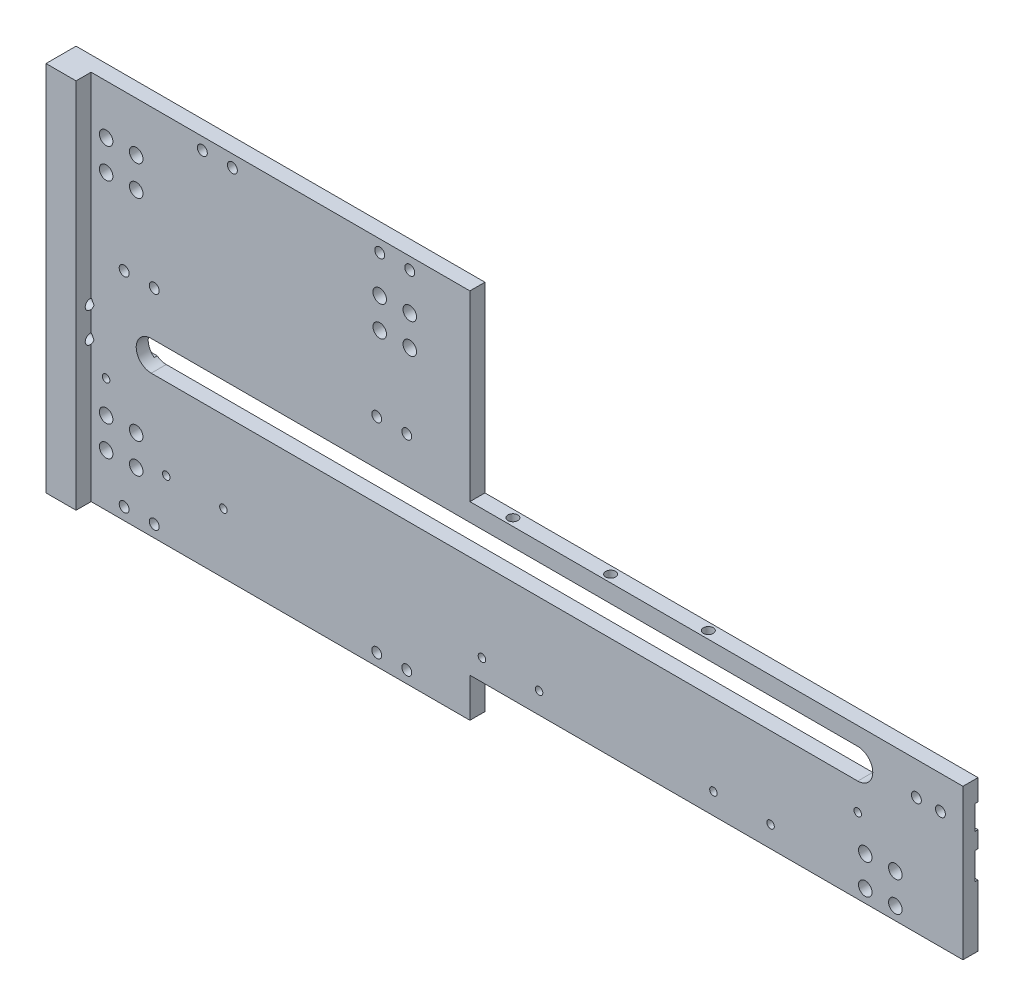
SolidWorks part; units mm, degrees
ref_plane "前视基准面" through (0, 0, 0) normal (0, 0, 1) x (1, 0, 0)
ref_plane "上视基准面" through (0, 0, 0) normal (0, 1, 0) x (1, 0, 0)
ref_plane "右视基准面" through (0, 0, 0) normal (1, 0, 0) x (0, 0, -1)
sketch "草图4" plane through (0, 0, 0) normal (0, 0, 1) x (1, 0, 0)
  line L0 (30, 99.7) -> (265, 99.7) construction
  line L1 (0, 0) -> (136, 0)
  line L2 (0, 0) -> (0, 123.7)
  line L3 (0, 123.7) -> (136, 123.7)
  line L4 (300, 60.7) -> (300, 110.7)
  line L5 (30, 104.7) -> (265, 104.7)
  line L6 (136, 123.7) -> (136, 110.7)
  line L7 (136, 110.7) -> (300, 110.7)
  line L9 (30, 94.7) -> (265, 94.7)
  line L10 (136, 0) -> (136, 60.7)
  line L11 (136, 60.7) -> (300, 60.7)
  arc A0 (30, 104.7) -> (30, 94.7) centre (30, 99.7) ccw
  arc A1 (265, 94.7) -> (265, 104.7) centre (265, 99.7) ccw
  dimension "D1" = 300
  dimension "D2" = 136
  dimension "D3" = 13
  dimension "D4" = 63
  dimension "D5" = 123.7
  dimension "D6" = 10
  dimension "D7" = 30
  dimension "D8" = 265
  dimension "D9" = 24
extrude "凸台-拉伸1" add sketch "草图4" along normal blind 10
sketch "草图5" plane through (300, 0, 0) normal (1, 0, 0) x (0, 0, -1)
  line L1 (0, 60.7) -> (0, 110.7) construction
  line L2 (-10, 123.7) -> (0, 123.7) construction
  line L3 (0, 103.7) -> (-1, 103.7)
  line L4 (0, 103.7) -> (0, 95.7)
  line L6 (0, 95.7) -> (-1, 95.7)
  line L7 (0, 90.2) -> (-1, 90.2)
  line L8 (0, 90.2) -> (0, 81.2)
  line L9 (0, 81.2) -> (-1, 81.2)
  line L10 (-1, 90.2) -> (-1, 81.2)
  line L12 (-1, 103.7) -> (-1, 95.7)
  dimension "D1" = 20
  dimension "D2" = 8
  dimension "D3" = 33.5
  dimension "D4" = 9
  dimension "D5" = 1
extrude "切除-拉伸1" cut sketch "草图5" against normal through all
hole_wizard "M4 螺纹孔1" positions "草图6" profile "草图7" tap size "M4" standard "ISO"
sketch "草图6" plane through (0, 0, 0) normal (-1, 0, 0) x (0, 0, 1)
  line L0 (10, 123.7) -> (10, 0) construction
  line L1 (10, 123.7) -> (0, 123.7) construction
  point P0 (5.304, 104.7)
  point P2 (5.304, 94.7)
  dimension "D1" = 4.696
  dimension "D2" = 19
  dimension "D3" = 29
sketch "草图7" plane through (0, 104.7, 5.304) normal (0, 1, 0) x (0, 0, 1)
  line L0 (0, 0) -> (0, 11.0914)
  line L1 (0, 11.0914) -> (1.65, 10.1)
  line L2 (1.65, 10.1) -> (1.65, 0)
  line L5 (1.65, 0) -> (0, 0)
  line L10 (0, 11.0914) -> (-1.65, 10.1) construction
  line L11 (0, -6.35) -> (0, 107.95) construction
  dimension "螺纹孔钻头直径" = 3.3
  dimension "螺纹孔钻头深度" = 10.1
  dimension "导头角度" = 118
cosmetic thread "孔螺蚊线1" parameters "D1"=8, "D2"=4
cosmetic thread "孔螺蚊线2" parameters "D1"=8, "D2"=4
sketch "草图8" plane through (0, 0, 10) normal (0, 0, 1) x (1, 0, 0)
  line L1 (136, 123.7) -> (0, 123.7) construction
  line L2 (10, 123.7) -> (316.5249, 123.7)
  line L3 (10, 123.7) -> (10, -39.0626)
  line L4 (10, -39.0626) -> (316.5249, -39.0626)
  line L5 (316.5249, 123.7) -> (316.5249, -39.0626)
  line L6 (0, 123.7) -> (0, 0) construction
  dimension "D1" = 10
extrude "切除-拉伸2" cut sketch "草图8" against normal blind 5
hole_wizard "M4 螺纹孔2" positions "草图9" profile "草图10" tap size "M4" standard "ISO"
sketch "草图9" plane through (0, 0, 5) normal (0, 0, 1) x (1, 0, 0)
  line L0 (136, 123.7) -> (10, 123.7) construction
  line L1 (0, 123.7) -> (0, 0) construction
  point P0 (21, 119.7)
  point P2 (31, 119.7)
  point P4 (105, 119.7)
  point P6 (115, 119.7)
  point P8 (21, 51.7)
  point P10 (31, 51.7)
  point P12 (105, 51.7)
  point P14 (115, 51.7)
  point P16 (47, 4)
  point P18 (57, 4)
  point P20 (106, 4)
  point P22 (116, 4)
  dimension "D1" = 4
  dimension "D2" = 72
  dimension "D3" = 119.7
  dimension "D4" = 21
  dimension "D5" = 31
  dimension "D6" = 105
  dimension "D7" = 115
  dimension "D8" = 47
  dimension "D9" = 57
  dimension "D10" = 106
  dimension "D11" = 116
sketch "草图10" plane through (21, 119.7, 5) normal (1, 0, 0) x (0, -1, 0)
  line L0 (0, 0) -> (0, 11.0914)
  line L1 (0, 11.0914) -> (1.65, 10.1)
  line L2 (1.65, 10.1) -> (1.65, 0)
  line L5 (1.65, 0) -> (0, 0)
  line L10 (0, 11.0914) -> (-1.65, 10.1) construction
  line L11 (0, -6.35) -> (0, 107.95) construction
  dimension "螺纹孔钻头直径" = 3.3
  dimension "螺纹孔钻头深度" = 10.1
  dimension "导头角度" = 118
cosmetic thread "孔螺蚊线3" parameters "D1"=5, "D2"=4
cosmetic thread "孔螺蚊线4" parameters "D1"=5, "D2"=4
cosmetic thread "孔螺蚊线5" parameters "D1"=5, "D2"=4
cosmetic thread "孔螺蚊线6" parameters "D1"=5, "D2"=4
cosmetic thread "孔螺蚊线7" parameters "D1"=5, "D2"=4
cosmetic thread "孔螺蚊线8" parameters "D1"=5, "D2"=4
cosmetic thread "孔螺蚊线9" parameters "D1"=5, "D2"=4
cosmetic thread "孔螺蚊线10" parameters "D1"=5, "D2"=4
cosmetic thread "孔螺蚊线11" parameters "D1"=5, "D2"=4
cosmetic thread "孔螺蚊线12" parameters "D1"=5, "D2"=4
cosmetic thread "孔螺蚊线13" parameters "D1"=5, "D2"=4
cosmetic thread "孔螺蚊线14" parameters "D1"=5, "D2"=4
hole_wizard "M3 螺纹孔1" positions "草图11" profile "草图12" tap size "M3" standard "ISO"
sketch "草图11" plane through (0, 0, 5) normal (0, 0, 1) x (1, 0, 0)
  line L0 (0, 123.7) -> (0, 0) construction
  line L1 (10, 123.7) -> (0, 123.7) construction
  point P0 (15, 85.7)
  point P2 (265, 85.7)
  dimension "D1" = 15
  dimension "D2" = 265
  dimension "D3" = 38
sketch "草图12" plane through (15, 85.7, 5) normal (1, 0, 0) x (0, -1, 0)
  line L0 (0, 0) -> (0, 8.2511)
  line L1 (0, 8.2511) -> (1.25, 7.5)
  line L2 (1.25, 7.5) -> (1.25, 0)
  line L5 (1.25, 0) -> (0, 0)
  line L10 (0, 8.2511) -> (-1.25, 7.5) construction
  line L11 (0, -6.35) -> (0, 107.95) construction
  dimension "螺纹孔钻头直径" = 2.5
  dimension "螺纹孔钻头深度" = 7.5
  dimension "导头角度" = 118
cosmetic thread "孔螺蚊线15" parameters "D1"=4, "D2"=3
cosmetic thread "孔螺蚊线16" parameters "D1"=4, "D2"=3
hole_wizard "M3 螺纹孔2" positions "草图13" profile "草图14" tap size "M3" standard "ISO"
sketch "草图13" plane through (0, 0, 5) normal (0, 0, 1) x (1, 0, 0)
  line L0 (136, 123.7) -> (10, 123.7) construction
  line L1 (0, 123.7) -> (0, 0) construction
  point P0 (35, 67.7)
  point P2 (54, 67.7)
  point P4 (140, 67.7)
  point P6 (159, 67.7)
  point P8 (217, 67.7)
  point P10 (236, 67.7)
  dimension "D1" = 56
  dimension "D2" = 35
  dimension "D3" = 54
  dimension "D4" = 140
  dimension "D5" = 159
  dimension "D6" = 217
  dimension "D7" = 236
sketch "草图14" plane through (35, 67.7, 5) normal (1, 0, 0) x (0, -1, 0)
  line L0 (0, 0) -> (0, 8.2511)
  line L1 (0, 8.2511) -> (1.25, 7.5)
  line L2 (1.25, 7.5) -> (1.25, 0)
  line L5 (1.25, 0) -> (0, 0)
  line L10 (0, 8.2511) -> (-1.25, 7.5) construction
  line L11 (0, -6.35) -> (0, 107.95) construction
  dimension "螺纹孔钻头直径" = 2.5
  dimension "螺纹孔钻头深度" = 7.5
  dimension "导头角度" = 118
cosmetic thread "孔螺蚊线17" parameters "D1"=5, "D2"=3
cosmetic thread "孔螺蚊线18" parameters "D1"=5, "D2"=3
cosmetic thread "孔螺蚊线19" parameters "D1"=5, "D2"=3
cosmetic thread "孔螺蚊线20" parameters "D1"=5, "D2"=3
cosmetic thread "孔螺蚊线21" parameters "D1"=5, "D2"=3
cosmetic thread "孔螺蚊线22" parameters "D1"=5, "D2"=3
sketch "草图15" plane through (0, 0, 5) normal (0, 0, 1) x (1, 0, 0)
  line L0 (0, 123.7) -> (0, 0) construction
  line L1 (136, 123.7) -> (10, 123.7) construction
  line L2 (20, 75) -> (20, 133.6461) construction
  line L3 (4.9076, 70) -> (26.7652, 70) construction
  circle A0 centre (15, 75) radius 2.25
  circle A1 centre (25, 75) radius 2.25
  circle A2 centre (25, 65) radius 2.25
  circle A3 centre (15, 65) radius 2.25
  dimension "D1" = 4.5
  dimension "D2" = 15
  dimension "D3" = 48.7
  dimension "D4" = 5
  dimension "D5" = 5
extrude "切除-拉伸3" cut sketch "草图15" against normal blind 5
pattern_linear "阵列(线性)1" count 2 spacing 252.5 along (1, 0, 0) of "切除-拉伸3"
pattern_linear "阵列(线性)2" count 2 spacing 35 along (0, -1, 0) of "切除-拉伸3"
pattern_linear "阵列(线性)3" count 2 spacing 100 along (1, 0, 0) of "阵列(线性)2", "切除-拉伸3"
sketch "草图16" plane through (0, 0, 5) normal (0, 0, 1) x (1, 0, 0)
  line L1 (105.3882, 81.0569) -> (130.1902, 81.0569)
  line L2 (105.3882, 81.0569) -> (105.3882, 58.9705)
  line L3 (105.3882, 58.9705) -> (130.1902, 58.9705)
  line L4 (130.1902, 81.0569) -> (130.1902, 58.9705)
extrude "凸台-拉伸2" add sketch "草图16" against normal up to surface (5 mm away) up to face at (122.75, 75, 0)
hole_wizard "M4 螺纹孔3" positions "草图17" profile "草图18" tap size "M4" standard "ISO"
sketch "草图17" plane through (0, 60.7, 0) normal (0, -1, 0) x (-1, 0, 0)
  line L0 (-136, -5) -> (-300, -5) construction
  line L1 (0, -10) -> (0, 0) construction
  point P0 (-147.8, -2.5)
  point P2 (-180.3, -2.5)
  point P4 (-212.8, -2.5)
  dimension "D1" = 2.5
  dimension "D2" = 147.8
  dimension "D3" = 180.3
  dimension "D4" = 212.8
sketch "草图18" plane through (147.8, 60.7, 2.5) normal (1, 0, 0) x (0, 0, -1)
  line L0 (0, 0) -> (0, 11.0914)
  line L1 (0, 11.0914) -> (1.65, 10.1)
  line L2 (1.65, 10.1) -> (1.65, 0)
  line L5 (1.65, 0) -> (0, 0)
  line L10 (0, 11.0914) -> (-1.65, 10.1) construction
  line L11 (0, -6.35) -> (0, 107.95) construction
  dimension "螺纹孔钻头直径" = 3.3
  dimension "螺纹孔钻头深度" = 10.1
  dimension "导头角度" = 118
cosmetic thread "孔螺蚊线23" parameters "D1"=8, "D2"=4
cosmetic thread "孔螺蚊线24" parameters "D1"=8, "D2"=4
cosmetic thread "孔螺蚊线25" parameters "D1"=8, "D2"=4
ref_plane "基准面1" through (0, 85.7, 0) normal (0, -1, 0) x (-1, 0, 0)
mirror "镜向1" about plane through (0, 85.7, 0) normal (0, -1, 0) of "M4 螺纹孔3"
hole_wizard "M4 螺纹孔4" positions "草图19" profile "草图20" tap size "M4" standard "ISO"
sketch "草图19" plane through (0, 0, 1) normal (0, 0, -1) x (-1, 0, 0)
  line L0 (-300, 103.7) -> (-300, 95.7) construction
  line L1 (-268, 95.7) -> (-300, 95.7) construction
  point P0 (-284.5, 99.7)
  point P2 (-292.5, 99.7)
  dimension "D1" = 8
  dimension "D2" = 7.5
  dimension "D3" = 4
sketch "草图20" plane through (284.5, 99.7, 1) normal (1, 0, 0) x (0, 1, 0)
  line L0 (0, 0) -> (0, 11.0914)
  line L1 (0, 11.0914) -> (1.65, 10.1)
  line L2 (1.65, 10.1) -> (1.65, 0)
  line L5 (1.65, 0) -> (0, 0)
  line L10 (0, 11.0914) -> (-1.65, 10.1) construction
  line L11 (0, -6.35) -> (0, 107.95) construction
  dimension "螺纹孔钻头直径" = 3.3
  dimension "螺纹孔钻头深度" = 10.1
  dimension "导头角度" = 118
cosmetic thread "孔螺蚊线26" parameters "D1"=4, "D2"=4
cosmetic thread "孔螺蚊线27" parameters "D1"=4, "D2"=4
sketch "草图21" plane through (0, 123.7, 0) normal (0, 1, 0) x (1, 0, 0)
  line L0 (0, -10) -> (0, 0)
  line L1 (0, 0) -> (136, 0)
  line L2 (136, 0) -> (136, -5)
  line L3 (136, -5) -> (10, -5)
  line L4 (10, -5) -> (10, -10)
  line L5 (10, -10) -> (0, -10)
extrude "凸台-拉伸3" add sketch "草图21" along normal blind 47.7
ref_plane "基准面2" through (0, 85.7, 0) normal (0, -1, 0) x (-1, 0, 0)
mirror "镜向2" about plane through (0, 85.7, 0) normal (0, -1, 0) of "M4 螺纹孔2"
sketch "草图24" plane through (0, 0, 0) normal (0, 0, -1) x (-1, 0, 0)
  line L0 (0, 81.2) -> (0, 0) construction
  line L1 (0, 47.7) -> (-146.6221, 47.7)
  line L2 (0, 47.7) -> (0, -36.9879)
  line L3 (0, -36.9879) -> (-146.6221, -36.9879)
  line L4 (-146.6221, 47.7) -> (-146.6221, -36.9879)
  line L5 (0, 47.7) -> (-134.6, 47.7) construction
extrude "切除-拉伸4" cut sketch "草图24" against normal blind 47.7
pattern_linear "阵列(线性)4" count 2 spacing 80 along (0, 1, 0) of "切除-拉伸3"
sketch "草图25" plane through (0, 0, 0) normal (0, 0, -1) x (-1, 0, 0)
  line L0 (-15, 145) -> (-147.186, 145) construction
  line L1 (-15, 155) -> (-147.186, 155) construction
  line L2 (-147.186, 145) -> (-147.186, 155) construction
  line L3 (-147.186, 155) -> (-147.186, 150) construction
  line L4 (-147.186, 150) -> (-114.2314, 150) construction
  line L5 (-136, 110.7) -> (-136, 171.4) construction
  circle A0 centre (-106, 145) radius 2.25
  circle A1 centre (-116, 145) radius 2.25
  circle A2 centre (-116, 155) radius 2.25
  circle A3 centre (-106, 155) radius 2.25
  point P10 (-116, 155)
  point P13 (-106, 155)
  dimension "D1" = 4.5
  dimension "D2" = 4.5
  dimension "D3" = 10
  dimension "D4" = 20
extrude "切除-拉伸5" cut sketch "草图25" against normal blind 10
